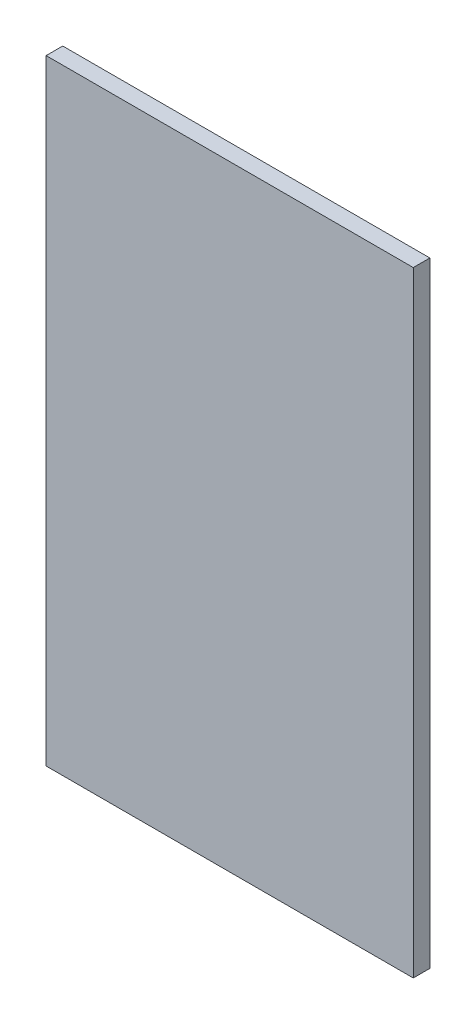
SolidWorks part; units mm, degrees
ref_plane "Front Plane" through (0, 0, 0) normal (0, 0, 1) x (1, 0, 0)
ref_plane "Top Plane" through (0, 0, 0) normal (0, 1, 0) x (1, 0, 0)
ref_plane "Right Plane" through (0, 0, 0) normal (1, 0, 0) x (0, 0, -1)
sketch "Sketch1" plane through (0, 0, 0) normal (0, 0, 1) x (1, 0, 0)
  line L1 (199, -333.5) -> (-199, -333.5)
  line L2 (199, -333.5) -> (199, 333.5)
  line L3 (199, 333.5) -> (-199, 333.5)
  line L4 (-199, -333.5) -> (-199, 333.5)
  line L5 (199, -333.5) -> (-199, 333.5) construction
  line L6 (199, 333.5) -> (-199, -333.5) construction
  point P0 (0, 0)
  dimension "D1" = 667
  dimension "D2" = 398
extrude "Boss-Extrude1" add sketch "Sketch1" along normal blind 18
equation "\"H_DSP\"=18"
equation "\"D1@Boss-Extrude1\"=\"H_DSP\""
